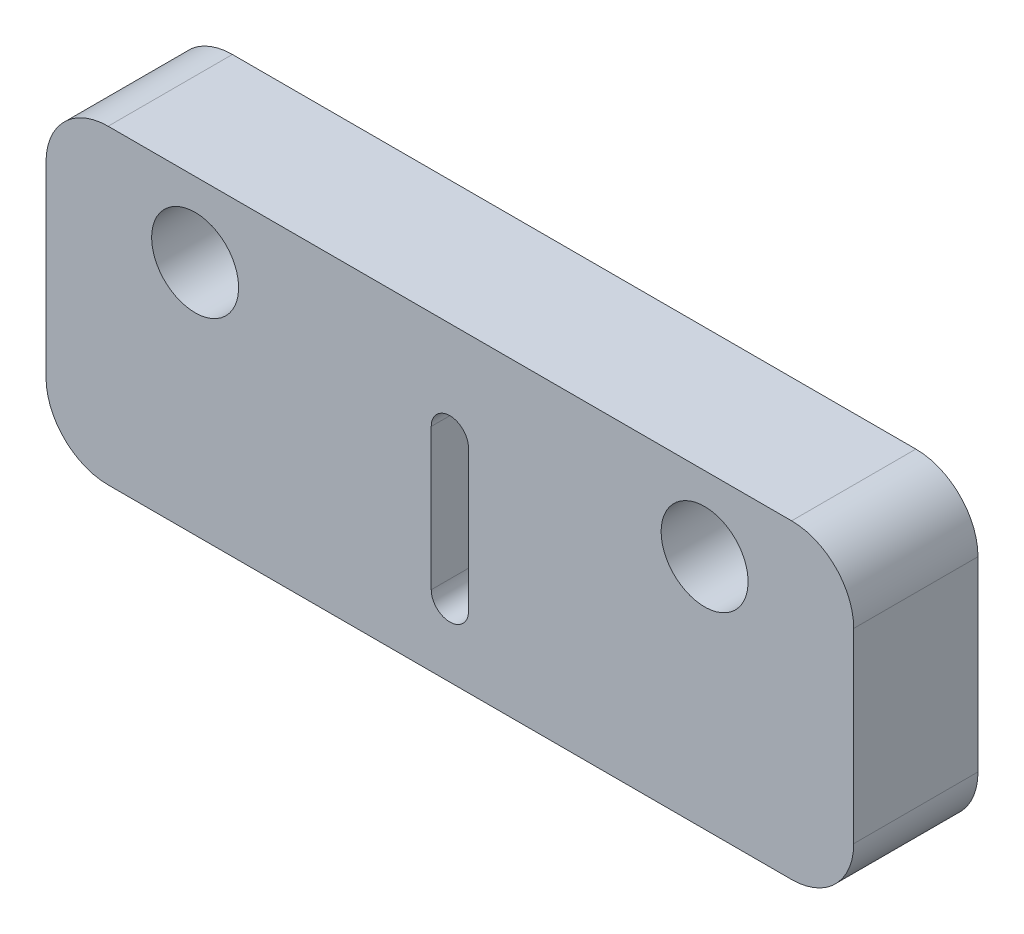
SolidWorks part; units mm, degrees
ref_plane "Front Plane" through (0, 0, 0) normal (0, 0, 1) x (1, 0, 0)
ref_plane "Top Plane" through (0, 0, 0) normal (0, 1, 0) x (1, 0, 0)
ref_plane "Right Plane" through (0, 0, 0) normal (1, 0, 0) x (0, 0, -1)
sketch "Sketch1" plane through (0, 0, 0) normal (0, 1, 0) x (1, 0, 0)
  line L1 (-30.1873, 10.3464) -> (34.8127, 10.3464)
  line L2 (-30.1873, 10.3464) -> (-30.1873, 0.3464)
  line L3 (-30.1873, 0.3464) -> (34.8127, 0.3464)
  line L4 (34.8127, 10.3464) -> (34.8127, 0.3464)
  dimension "D1" = 65
  dimension "D2" = 10
extrude "Boss-Extrude1" add sketch "Sketch1" along normal blind 25
sketch "Sketch2" plane through (0, 0, -10.3464) normal (0, 0, -1) x (-1, 0, 0)
  line L0 (-34.8127, 25) -> (30.1873, 25) construction
  line L1 (-2.3127, 25) -> (-2.3127, 0) construction
  line L2 (-34.8127, 0) -> (30.1873, 0) construction
  line L3 (-2.3127, 17.077) -> (-2.3127, 5.6962) construction
  line L4 (-0.8127, 17.077) -> (-0.8127, 5.6962)
  line L5 (-3.8127, 17.077) -> (-3.8127, 5.6962)
  circle A0 centre (-22.8127, 19) radius 3.5
  circle A1 centre (18.1873, 19) radius 3.5
  arc A2 (-0.8127, 17.077) -> (-3.8127, 17.077) centre (-2.3127, 17.077) ccw
  arc A3 (-3.8127, 5.6962) -> (-0.8127, 5.6962) centre (-2.3127, 5.6962) ccw
  point P12 (-2.3127, 11.3866)
  point P17 (-2.3127, 5.6962)
  point P18 (-2.3127, 17.077)
  dimension "D1" = 7
  dimension "D2" = 6
  dimension "D3" = 6
  dimension "D4" = 41
  dimension "D5" = 20.5
extrude "Cut-Extrude1" cut sketch "Sketch2" against normal blind 25 contours A1 | L5 A3 L4 A2 | A0
fillet "Fillet1" radius 5 4 edges at (-30.1873, 0, -5.3464) (34.8127, 0, -5.3464) (34.8127, 25, -5.3464) (-30.1873, 25, -5.3464)
